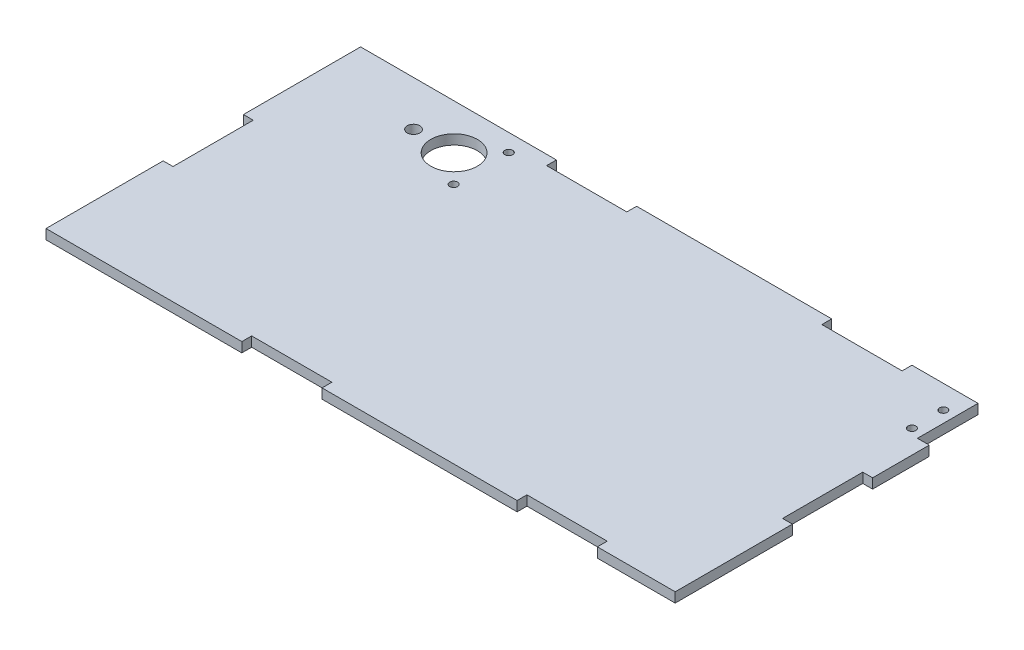
SolidWorks part; units mm, degrees
ref_plane "Front Plane" through (0, 0, 0) normal (0, 0, 1) x (1, 0, 0)
ref_plane "Top Plane" through (0, 0, 0) normal (0, 1, 0) x (1, 0, 0)
ref_plane "Right Plane" through (0, 0, 0) normal (1, 0, 0) x (0, 0, -1)
sketch "Sketch1" plane through (0, 0, 0) normal (0, 1, 0) x (1, 0, 0)
  line L1 (-75.3241, 50.3621) -> (127.8759, 50.3621)
  line L2 (-75.3241, 50.3621) -> (-75.3241, -51.2379)
  line L3 (-75.3241, -51.2379) -> (127.8759, -51.2379)
  line L4 (127.8759, 50.3621) -> (127.8759, -51.2379)
  circle A9 centre (120.3572, 32.7091) radius 1.27
  circle A10 centre (120.3572, 42.8691) radius 1.27
  circle A11 centre (-30.6091, 35.8371) radius 7.5184
  circle A18 centre (-43.7091, 35.8371) radius 2.032
  circle A19 centre (-21.8591, 44.7371) radius 1.27
  circle A20 centre (-21.8591, 26.9371) radius 1.27
  dimension "D3" = 2.54
  dimension "D4" = 2.54
  dimension "D5" = 15.0368
  dimension "D6" = 4.064
  dimension "D7" = 2.54
  dimension "D8" = 2.54
  dimension "D1" = 101.6
  dimension "D2" = 203.2
extrude "Boss-Extrude1" add sketch "Sketch1" along normal blind 3.175
sketch "Sketch2" plane through (0, 0, -50.3621) normal (0, 0, -1) x (-1, 0, 0)
  line L0 (-127.8759, 3.175) -> (75.3241, 3.175) construction
  line L1 (-102.7299, 3.175) -> (-76.8219, 3.175)
  line L2 (-102.7299, 3.175) -> (-102.7299, 0)
  line L3 (-102.7299, 0) -> (-76.8219, 0)
  line L4 (-76.8219, 3.175) -> (-76.8219, 0)
  line L5 (-127.8759, 0) -> (75.3241, 0) construction
  line L6 (75.3241, 3.175) -> (75.3241, 0) construction
  line L7 (-13.8299, 3.175) -> (12.0781, 3.175)
  line L8 (-13.8299, 3.175) -> (-13.8299, 0)
  line L9 (-13.8299, 0) -> (12.0781, 0)
  line L10 (12.0781, 3.175) -> (12.0781, 0)
  dimension "D1" = 25.908
  dimension "D2" = 25.908
  dimension "D3" = 63.246
  dimension "D4" = 62.992
extrude "Cut-Extrude1" cut sketch "Sketch2" against normal blind 3.175
sketch "Sketch3" plane through (0, 0, 51.2379) normal (0, 0, 1) x (1, 0, 0)
  line L0 (-75.3241, 0) -> (127.8759, 0) construction
  line L1 (13.8299, 0) -> (-12.0781, 0)
  line L2 (13.8299, 0) -> (13.8299, 3.175)
  line L3 (13.8299, 3.175) -> (-12.0781, 3.175)
  line L4 (-12.0781, 0) -> (-12.0781, 3.175)
  line L5 (-75.3241, 3.175) -> (127.8759, 3.175) construction
  line L7 (102.7299, 0) -> (76.8219, 0)
  line L8 (102.7299, 0) -> (102.7299, 3.175)
  line L9 (102.7299, 3.175) -> (76.8219, 3.175)
  line L10 (76.8219, 0) -> (76.8219, 3.175)
  dimension "D1" = 25.908
  dimension "D2" = 25.908
extrude "Cut-Extrude2" cut sketch "Sketch3" against normal blind 3.175
sketch "Sketch5" plane through (-75.3241, 0, 0) normal (-1, 0, 0) x (0, 0, 1)
  line L0 (-50.3621, 3.175) -> (51.2379, 3.175) construction
  line L1 (13.3919, 3.175) -> (-12.5161, 3.175)
  line L2 (13.3919, 3.175) -> (13.3919, 0)
  line L3 (13.3919, 0) -> (-12.5161, 0)
  line L4 (-12.5161, 3.175) -> (-12.5161, 0)
  line L5 (-50.3621, 0) -> (51.2379, 0) construction
  line L6 (51.2379, 3.175) -> (51.2379, 0) construction
  dimension "D1" = 25.908
  dimension "D2" = 37.846
extrude "Cut-Extrude3" cut sketch "Sketch5" against normal blind 3.175
sketch "Sketch6" plane through (127.8759, 0, 0) normal (1, 0, 0) x (0, 0, -1)
  line L0 (-51.2379, 0) -> (50.3621, 0) construction
  line L1 (-13.3919, 0) -> (12.5161, 0)
  line L2 (-13.3919, 0) -> (-13.3919, 3.175)
  line L3 (-13.3919, 3.175) -> (12.5161, 3.175)
  line L4 (12.5161, 0) -> (12.5161, 3.175)
  line L5 (-51.2379, 3.175) -> (50.3621, 3.175) construction
  line L6 (-51.2379, 3.175) -> (-51.2379, 0) construction
  dimension "D1" = 25.908
  dimension "D2" = 37.846
extrude "Cut-Extrude4" cut sketch "Sketch6" against normal blind 3.175
sketch "Sketch7" plane through (0, 0, 0) normal (0, -1, 0) x (1, 0, 0)
  line L1 (127.8759, -50.3621) -> (124.0659, -50.3621)
  line L2 (127.8759, -50.3621) -> (127.8759, -30.8041)
  line L3 (127.8759, -30.8041) -> (124.0659, -30.8041)
  line L4 (124.0659, -50.3621) -> (124.0659, -30.8041)
  dimension "D1" = 19.558
  dimension "D2" = 3.81
extrude "Cut-Extrude5" cut sketch "Sketch7" against normal blind 3.175
